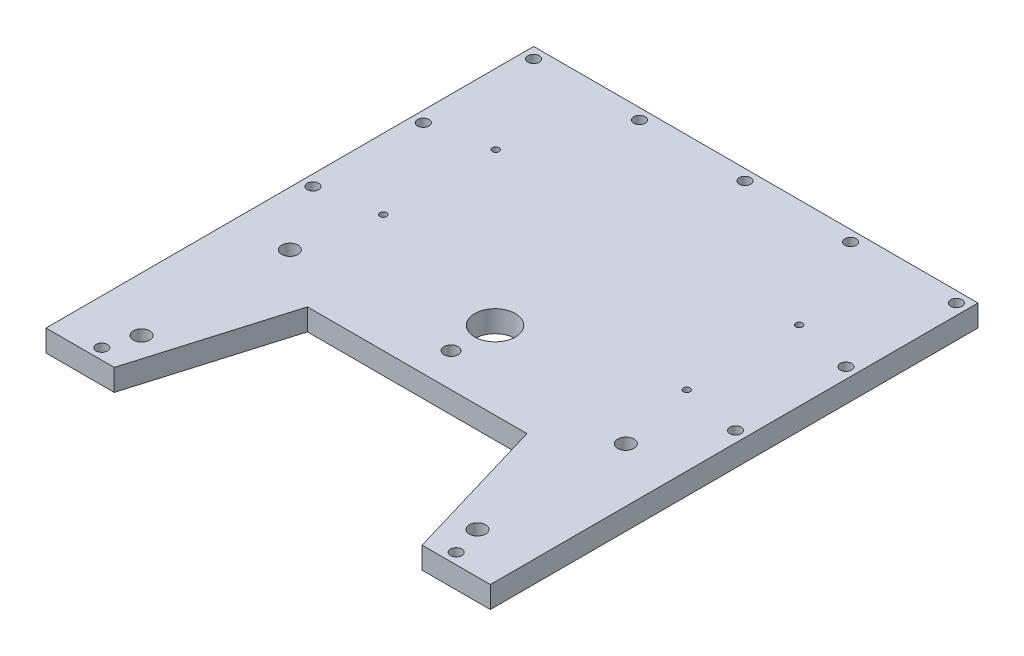
SolidWorks part; units mm, degrees
ref_plane "Front Plane" through (0, 0, 0) normal (0, 0, 1) x (1, 0, 0)
ref_plane "Top Plane" through (0, 0, 0) normal (0, 1, 0) x (1, 0, 0)
ref_plane "Right Plane" through (0, 0, 0) normal (1, 0, 0) x (0, 0, -1)
sketch "Sketch1" plane through (0, 0, 0) normal (0, 1, 0) x (1, 0, 0)
  line L0 (85, -185) -> (40.5, -35)
  line L1 (-82, 90) -> (82, 90)
  line L2 (-82, 90) -> (-82, -90)
  line L3 (-82, -90) -> (82, -90)
  line L4 (82, 90) -> (82, -90)
  line L5 (-82, 90) -> (82, -90) construction
  line L6 (-82, -90) -> (82, 90) construction
  line L7 (-40.5, -35) -> (-85, -185)
  line L8 (85, -185) -> (-85, -185)
  line L9 (40.5, -35) -> (-40.5, -35)
  line L10 (0, 90) -> (0, -90) construction
  point P0 (0, 0)
  point P8 (0, -35)
  point P13 (0, -185)
  dimension "D1" = 164
  dimension "D2" = 180
  dimension "D3" = 81
  dimension "D4" = 85
  dimension "D5" = 55
  dimension "D6" = 85
  dimension "D7" = 150
extrude "Boss-Extrude3" add sketch "Sketch1" along normal blind 8 contours L9 L0 L3 L4 L1 L2 L7
sketch "Sketch3" plane through (-73, 8, 0) normal (0, 1, 0) x (0, 0, 1)
  line L0 (-90, -9) -> (-0.5, -9)
  line L1 (-90, 73) -> (35, 73) construction
  line L2 (-90, -1) -> (-0.5, -1)
  line L12 (-90, -9) -> (-90, 155) construction
  line L18 (35, 113.5) -> (35, 32.5) construction
  line L23 (-0.5, -9) -> (-0.5, 155) construction
  line L24 (-90, -9) -> (-0.5, -9)
  line L25 (-90, -9) -> (-90, -1)
  line L26 (-90, -1) -> (-0.5, -1)
  line L27 (-0.5, -9) -> (-0.5, -1)
  line L28 (-90, 155) -> (90, 155) construction
  line L29 (-90, -5) -> (-0.5, -5) construction
  line L34 (-90, 151) -> (-0.5, 151) construction
  line L37 (-90, 147) -> (-0.5, 147)
  line L38 (-90, 147) -> (-82, 147)
  line L39 (-90, 147) -> (-90, -1)
  line L40 (-90, -1) -> (-82, -1)
  line L41 (-82, 147) -> (-82, -1)
  line L42 (-86, -1) -> (-86, 147) construction
  line L43 (-0.5, 155) -> (-0.5, 147)
  line L44 (-90, 155) -> (-0.5, 155)
  line L45 (-90, 155) -> (-90, 147)
  line L51 (35, 32.5) -> (90, 16.1833) construction
  line L52 (90, -9) -> (82, -9)
  line L53 (90, -9) -> (90, 18.5567)
  line L54 (90, 18.5567) -> (82, 18.5567)
  line L55 (82, -9) -> (82, 18.5567)
  circle A11 centre (-45.25, -5) radius 2.1
  circle A25 centre (-86, -5) radius 2.1
  circle A26 centre (-86, 34) radius 2.1
  circle A27 centre (-86, 73) radius 2.1
  circle A28 centre (-86, 112) radius 2.1
  circle A29 centre (-86, 151) radius 2.1
  circle A30 centre (-4.5, -5) radius 2.1
  circle A31 centre (-4.5, 151) radius 2.1
  circle A32 centre (-45.25, 151) radius 2.1
  circle A33 centre (86, 7.59) radius 2.1
  circle A34 centre (86, 138.41) radius 2.1
  point P38 (-82, 73)
  dimension "D1" = 8
  dimension "D2" = 89.5
  dimension "D4" = 4.2
  dimension "D3" = 8
  dimension "D5" = 40.75
  dimension "D6" = 5
  dimension "D7" = 4
  dimension "D8" = 8
  dimension "D9" = 4
  dimension "D10" = 16.59
extrude "Cut-Extrude2" cut sketch "Sketch3" against normal blind 10
sketch "Sketch5" plane through (0, 8, 0) normal (0, 1, 0) x (1, 0, 0)
  line L0 (82, 90) -> (82, -90) construction
  line L1 (56.8167, -90) -> (82, -90) construction
  line L2 (0, 90) -> (0, -35) construction
  line L3 (-82, 90) -> (82, 90) construction
  line L4 (40.5, -35) -> (-40.5, -35) construction
  circle A0 centre (62, -74.75) radius 3
  circle A1 centre (62, -19.99) radius 3
  circle A2 centre (-62, -74.75) radius 3
  circle A3 centre (-62, -19.99) radius 3
  circle A4 centre (0, -6.25) radius 7.5
  circle A5 centre (0, -22.5) radius 2.6
  dimension "D1" = 6
  dimension "D5" = 15
  dimension "D7" = 5.2
  dimension "D2" = 20
  dimension "D3" = 15.25
  dimension "D4" = 54.76
  dimension "D6" = 28.75
  dimension "D8" = 16.25
extrude "Cut-Extrude3" cut sketch "Sketch5" against normal up to next contours A2 | A3 | A0 | A1 | A4 | A5
sketch "Sketch6" plane through (0, 8, 0) normal (0, 1, 0) x (1, 0, 0)
  line L0 (0, 90) -> (0, -35) construction
  line L1 (-82, 90) -> (82, 90) construction
  line L2 (40.5, -35) -> (-40.5, -35) construction
  line L3 (-60, 29.25) -> (0, 29.25) construction
  line L4 (-60, 4.5) -> (-60, 54)
  line L5 (-60, 4.5) -> (60, 4.5)
  line L6 (60, 4.5) -> (60, 54)
  line L7 (-60, 54) -> (60, 54)
  line L8 (-60, 4.5) -> (60, 54) construction
  line L9 (60, 4.5) -> (-60, 54) construction
  circle A0 centre (-56, 8.5) radius 1.25
  circle A1 centre (-56, 50) radius 1.25
  circle A4 centre (56, 50) radius 1.25
  circle A5 centre (56, 8.5) radius 1.25
  point P6 (0, 29.25)
  point P23 (0, 54)
  dimension "D2" = 2.5
  dimension "D1" = 4
  dimension "D3" = 120
  dimension "D4" = 49.5
  dimension "D5" = 36
extrude "Cut-Extrude4" cut sketch "Sketch6" against normal up to next contours A1 | A0 | A5 | A4
